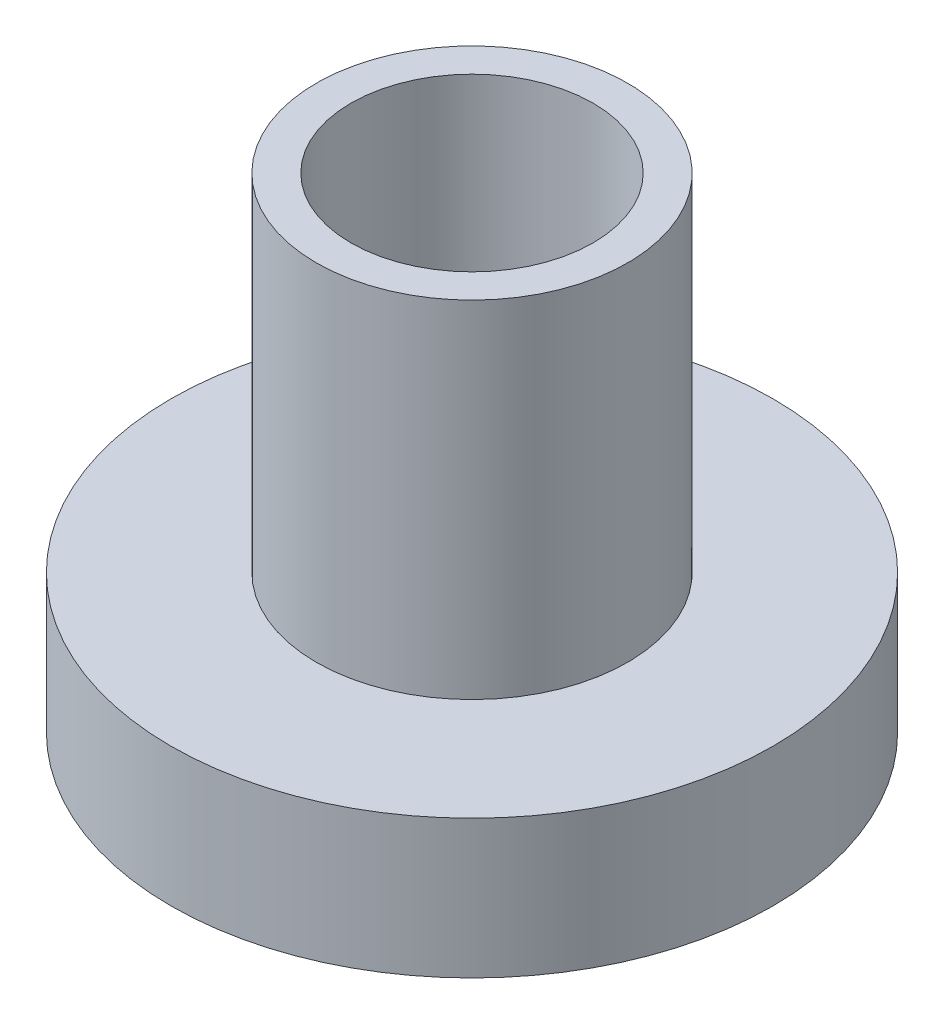
SolidWorks part; units mm, degrees
ref_plane "Front Plane" through (0, 0, 0) normal (0, 0, 1) x (1, 0, 0)
ref_plane "Top Plane" through (0, 0, 0) normal (0, 1, 0) x (1, 0, 0)
ref_plane "Right Plane" through (0, 0, 0) normal (1, 0, 0) x (0, 0, -1)
sketch "Sketch1" plane through (0, 0, 0) normal (0, 1, 0) x (1, 0, 0)
  circle A0 centre (0, 0) radius 4.35
  dimension "D1" = 8.7
extrude "Boss-Extrude1" add sketch "Sketch1" along normal blind 2
sketch "Sketch2" plane through (0, 2, 0) normal (0, 1, 0) x (1, 0, 0)
  circle A0 centre (0, 0) radius 2.25
  dimension "D1" = 4.5
extrude "Boss-Extrude2" add sketch "Sketch2" along normal blind 5
sketch "Sketch3" plane through (0, 7, 0) normal (0, 1, 0) x (1, 0, 0)
  circle A0 centre (0, 0) radius 1.75
  dimension "D1" = 3.5
extrude "Cut-Extrude1" cut sketch "Sketch3" against normal through all
